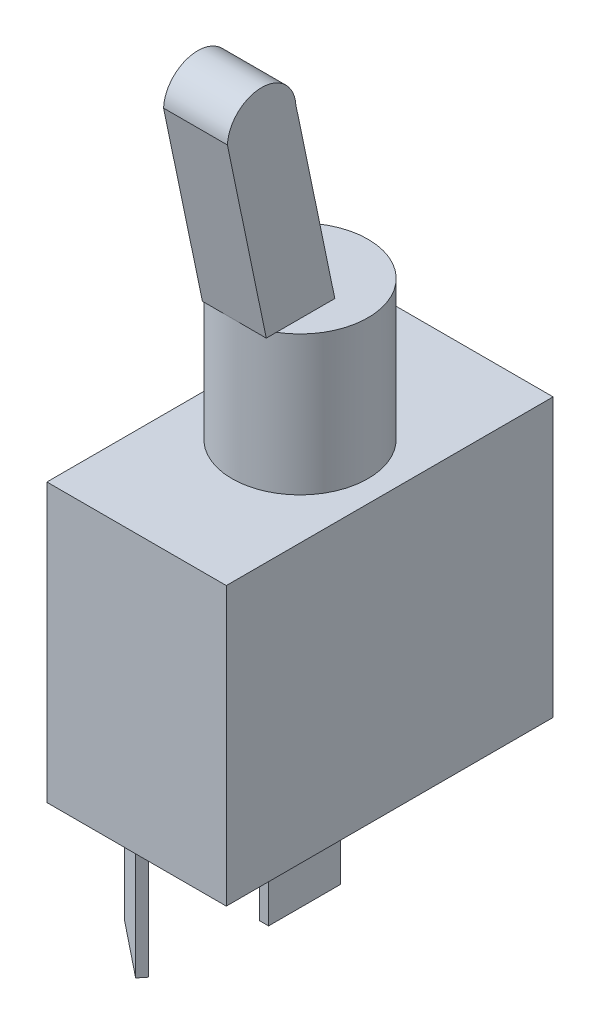
SolidWorks part; units mm, degrees
ref_plane "Front Plane" through (0, 0, 0) normal (0, 0, 1) x (1, 0, 0)
ref_plane "Top Plane" through (0, 0, 0) normal (0, 1, 0) x (1, 0, 0)
ref_plane "Right Plane" through (0, 0, 0) normal (1, 0, 0) x (0, 0, -1)
sketch "Sketch1" plane through (0, 0, 0) normal (0, 1, 0) x (1, 0, 0)
  line L1 (-7.85, 14.3) -> (7.85, 14.3)
  line L2 (-7.85, 14.3) -> (-7.85, -14.3)
  line L3 (-7.85, -14.3) -> (7.85, -14.3)
  line L4 (7.85, 14.3) -> (7.85, -14.3)
  line L5 (-7.85, 14.3) -> (7.85, -14.3) construction
  line L6 (-7.85, -14.3) -> (7.85, 14.3) construction
  point P0 (0, 0)
  dimension "D1" = 28.6
  dimension "D2" = 15.7
extrude "Body" add sketch "Sketch1" along normal blind 24.3
sketch "Sketch2" plane through (0, 24.3, 0) normal (0, 1, 0) x (1, 0, 0)
  circle A0 centre (0, 0) radius 5.9531
  dimension "D1" = 11.9062
extrude "Panel Mount  15/32" add sketch "Sketch2" along normal blind 12.2
sketch "Sketch9" plane through (0, 0, 0) normal (1, 0, 0) x (0, 0, -1)
  line L0 (0, 36.5) -> (-6, 36.5)
  line L1 (5.9531, 36.5) -> (-5.9531, 36.5) construction
  line L5 (0, 36.5) -> (-3.41, 52.886)
  line L6 (-6, 36.5) -> (-9.4008, 52.8421)
  arc A1 (-3.41, 52.886) -> (-9.4008, 52.8421) centre (-6.4042, 52.7) ccw
  dimension "D2" = 3
  dimension "D1" = 6
  dimension "D3" = 16.2
extrude "Switch" add sketch "Sketch9" along normal blind 3.048 and the other way blind 2.54
sketch "Sketch10" plane through (0, 0, 0) normal (0, -1, 0) x (1, 0, 0)
  line L0 (-6.3909, 8.9768) -> (-5.8912, 8.3521)
  line L1 (-0.4, 3.15) -> (0.4, 3.15)
  line L2 (-0.4, 3.15) -> (-0.4, -3.15)
  line L3 (-0.4, -3.15) -> (0.4, -3.15)
  line L4 (0.4, 3.15) -> (0.4, -3.15)
  line L5 (-6.3909, 8.9768) -> (-1.4715, 12.9124)
  line L6 (-5.8912, 8.3521) -> (-0.9717, 12.2877)
  line L7 (-1.4715, 12.9124) -> (-0.9717, 12.2877)
  line L8 (-6.3909, 8.9768) -> (-0.9717, 12.2877) construction
  line L9 (-5.8912, 8.3521) -> (-1.4715, 12.9124) construction
  line L11 (-0.4, 3.15) -> (0.4, -3.15) construction
  point P5 (-3.6813, 10.6322)
  dimension "D1" = 6.3
  dimension "D2" = 0.8
  dimension "D3" = 6.3
  dimension "D4" = 0.8
extrude "Connectors" add sketch "Sketch10" along normal blind 10.8
